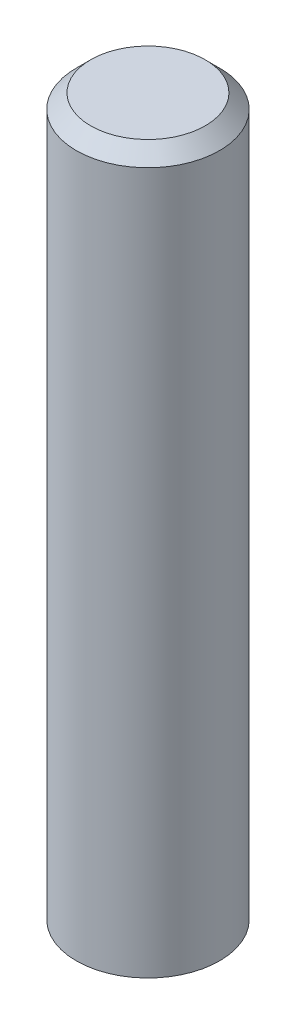
SolidWorks part; units mm, degrees
ref_plane "Piano frontale" through (0, 0, 0) normal (0, 0, 1) x (1, 0, 0)
ref_plane "Piano superiore" through (0, 0, 0) normal (0, 1, 0) x (1, 0, 0)
ref_plane "Piano destro" through (0, 0, 0) normal (1, 0, 0) x (0, 0, -1)
sketch "Schizzo1" plane through (0, 0, 0) normal (0, 1, 0) x (1, 0, 0)
  circle A0 centre (0, 0) radius 0.5
  dimension "D1" = 1
extrude "Estrusione-Estrusione1" add sketch "Schizzo1" along normal mid plane 5
chamfer "Smusso1" distance 0.1 angle 45 1 edges at (0, 2.5, 0.5)
